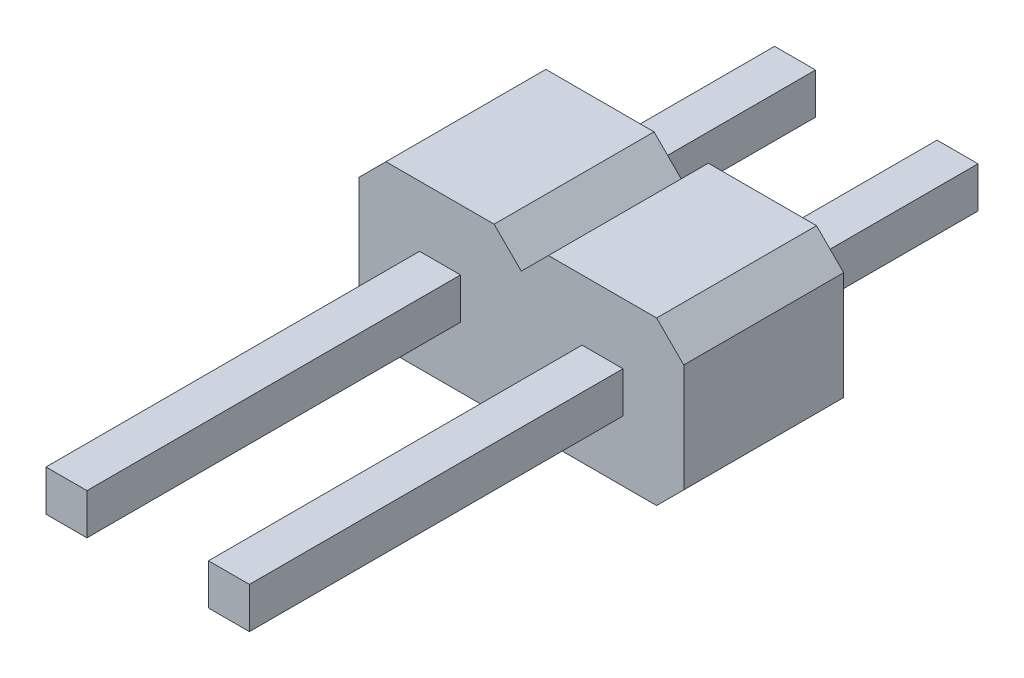
SolidWorks part; units mm, degrees
ref_plane "Front Plane" through (0, 0, 0) normal (0, 0, 1) x (1, 0, 0)
ref_plane "Top Plane" through (0, 0, 0) normal (0, 1, 0) x (1, 0, 0)
ref_plane "Right Plane" through (0, 0, 0) normal (1, 0, 0) x (0, 0, -1)
sketch "peg base" plane through (0, 0, 0) normal (0, 0, 1) x (1, 0, 0)
  line L0 (0.8457, -1.27) -> (1.27, -0.8457)
  line L1 (-0.8457, 1.27) -> (0.8457, 1.27)
  line L2 (-1.27, 0.8457) -> (-1.27, -0.8457)
  line L3 (-0.8457, -1.27) -> (0.8457, -1.27)
  line L4 (1.27, 0.8457) -> (1.27, -0.8457)
  line L6 (1.27, 0.8457) -> (0.8457, 1.27)
  line L7 (-0.8457, 1.27) -> (-1.27, 0.8457)
  line L8 (-1.27, -0.8457) -> (-0.8457, -1.27)
  line L9 (-2.9147, 0.9751) -> (-1.0815, 2.8082) construction
  line L10 (1.6011, 2.692) -> (3.2276, 1.0655) construction
  point P5 (0, 1.27)
  point P6 (1.27, 0)
  dimension "D1" = 0.6
  dimension "D2" = 2.54
extrude "peg" add sketch "peg base" along normal blind 2.5
sketch "tail base" plane through (0, 0, 0) normal (0, 0, -1) x (-1, 0, 0)
  line L1 (0.32, 0.32) -> (-0.32, 0.32)
  line L2 (0.32, 0.32) -> (0.32, -0.32)
  line L3 (0.32, -0.32) -> (-0.32, -0.32)
  line L4 (-0.32, 0.32) -> (-0.32, -0.32)
  point P4 (-0.32, 0)
  point P5 (0, -0.32)
  dimension "D1" = 0.64
  dimension "D2" = 0.64
extrude "tail" add sketch "tail base" along normal blind 3.05
sketch "head base" plane through (0, 0, 2.5) normal (0, 0, 1) x (1, 0, 0)
  line L1 (-0.32, 0.32) -> (0.32, 0.32)
  line L2 (-0.32, 0.32) -> (-0.32, -0.32)
  line L3 (-0.32, -0.32) -> (0.32, -0.32)
  line L4 (0.32, 0.32) -> (0.32, -0.32)
  point P4 (0, -0.32)
  point P5 (0.32, 0)
  dimension "D1" = 0.64
  dimension "D2" = 0.64
extrude "head" add sketch "head base" along normal blind 5.84
pattern_linear "multiply" count 2 spacing 2.54 along (1, 0, 0) of "tail", "head", "peg"
equation "\"pin_side_length\"=0.64"
equation "\"D2@tail base\"=\"pin_side_length\""
equation "\"D1@tail base\"=\"pin_side_length\""
equation "\"D1@head base\"=\"pin_side_length\""
equation "\"D2@head base\"=\"pin_side_length\""
